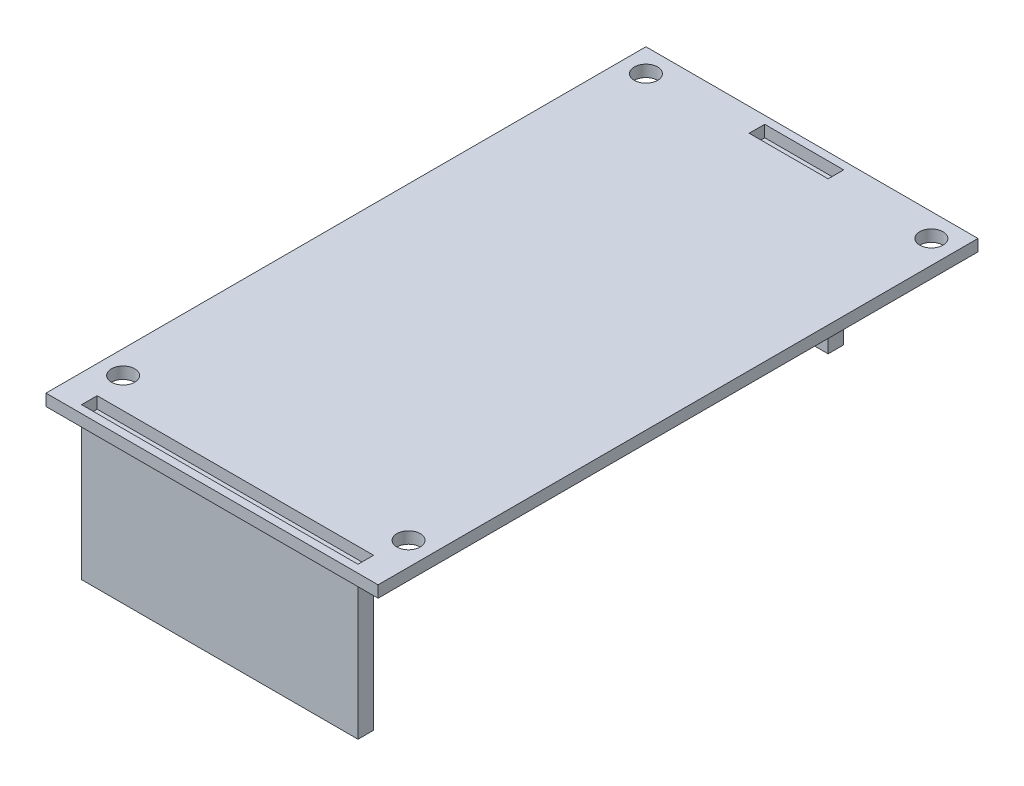
SolidWorks part; units mm, degrees
ref_plane "Front Plane" through (0, 0, 0) normal (0, 0, 1) x (1, 0, 0)
ref_plane "Top Plane" through (0, 0, 0) normal (0, 1, 0) x (1, 0, 0)
ref_plane "Right Plane" through (0, 0, 0) normal (1, 0, 0) x (0, 0, -1)
sketch "Sketch1" plane through (0, 0, 0) normal (0, 1, 0) x (1, 0, 0)
  line L1 (0, 0) -> (42.72, 0)
  line L2 (0, 0) -> (0, 77.18)
  line L3 (0, 77.18) -> (42.72, 77.18)
  line L4 (42.72, 0) -> (42.72, 77.18)
  line L5 (0, 0) -> (42.72, 77.18) construction
  line L6 (0, 77.18) -> (42.72, 0) construction
  line L7 (3.58, 1) -> (39.14, 1)
  line L8 (3.58, 1) -> (3.58, 3)
  line L9 (3.58, 3) -> (39.14, 3)
  line L10 (39.14, 1) -> (39.14, 3)
  line L11 (3.58, 1) -> (39.14, 3) construction
  line L12 (3.58, 3) -> (39.14, 1) construction
  line L13 (16.28, 76.18) -> (26.44, 76.18)
  line L14 (16.28, 76.18) -> (16.28, 74.18)
  line L15 (16.28, 74.18) -> (26.44, 74.18)
  line L16 (26.44, 76.18) -> (26.44, 74.18)
  line L17 (16.28, 76.18) -> (26.44, 74.18) construction
  line L18 (16.28, 74.18) -> (26.44, 76.18) construction
  circle A0 centre (39.72, 74.18) radius 1.5
  circle A1 centre (3, 74.18) radius 1.5
  circle A2 centre (3, 6.92) radius 1.5
  circle A3 centre (39.72, 6.92) radius 1.5
  point P4 (21.36, 38.59)
  point P18 (21.36, 2)
  point P24 (21.36, 75.18)
  dimension "D3" = 3
  dimension "D4" = 3
  dimension "D5" = 3
  dimension "D6" = 3
  dimension "D1" = 42.72
  dimension "D2" = 77.18
  dimension "D7" = 6.92
  dimension "D8" = 6.92
  dimension "D9" = 3
  dimension "D10" = 3
  dimension "D11" = 3
  dimension "D12" = 3
  dimension "D13" = 3
  dimension "D14" = 3
  dimension "D15" = 35.56
  dimension "D16" = 3.58
  dimension "D18" = 2
  dimension "D19" = 10.16
  dimension "D20" = 2
  dimension "D21" = 2
  dimension "D22" = 16.28
extrude "Boss-Extrude1" add sketch "Sketch1" along normal blind 1.5
sketch "Sketch2" plane through (0, 0, 0) normal (0, -1, 0) x (1, 0, 0)
  line L1 (39.14, -1) -> (3.58, -1)
  line L2 (39.14, -1) -> (39.14, -3)
  line L3 (39.14, -3) -> (3.58, -3)
  line L4 (3.58, -1) -> (3.58, -3)
  line L5 (39.14, -1) -> (3.58, -3) construction
  line L6 (39.14, -3) -> (3.58, -1) construction
  point P4 (21.36, -2)
extrude "Boss-Extrude2" add sketch "Sketch2" along normal blind 18 separate body
sketch "Sketch3" plane through (0, 0, 0) normal (0, -1, 0) x (1, 0, 0)
  line L0 (16.28, -76.18) -> (16.28, -74.18) construction
  line L1 (26.44, -74.18) -> (16.28, -74.18)
  line L2 (26.44, -74.18) -> (26.44, -76.18)
  line L3 (26.44, -76.18) -> (16.28, -76.18)
  line L4 (16.28, -74.18) -> (16.28, -76.18)
  line L5 (26.44, -74.18) -> (16.28, -76.18) construction
  line L6 (26.44, -76.18) -> (16.28, -74.18) construction
  point P4 (21.36, -75.18)
extrude "Boss-Extrude3" add sketch "Sketch3" along normal blind 18 separate body
